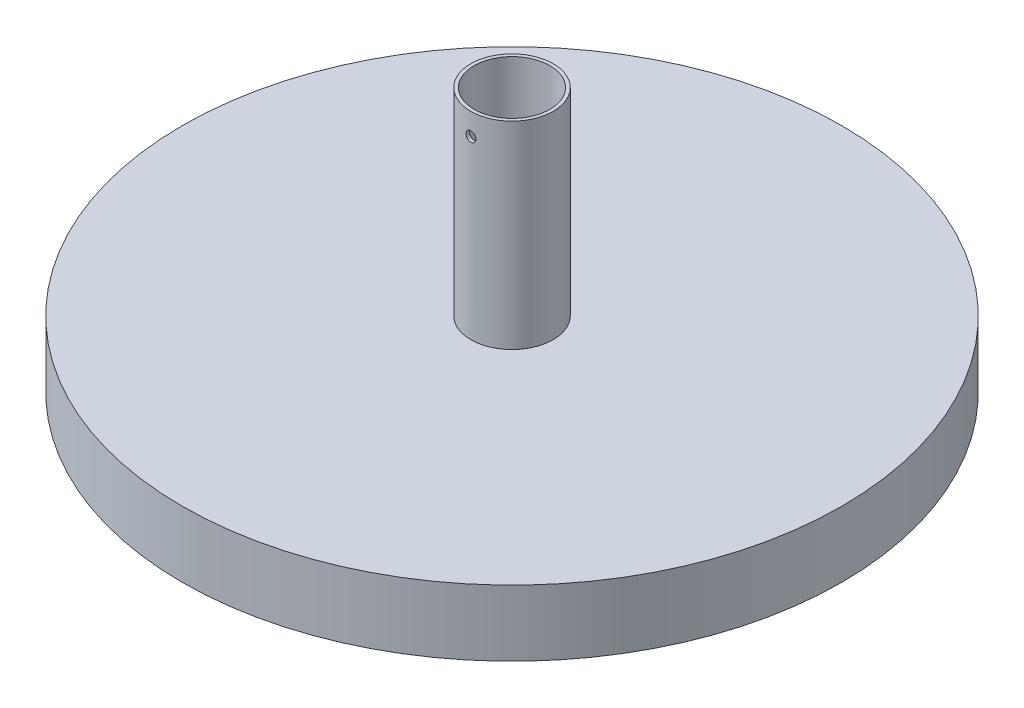
SolidWorks part; units mm, degrees
material "ABS"
ref_plane "Front Plane" through (0, 0, 0) normal (0, 0, 1) x (1, 0, 0)
ref_plane "Top Plane" through (0, 0, 0) normal (0, 1, 0) x (1, 0, 0)
ref_plane "Right Plane" through (0, 0, 0) normal (1, 0, 0) x (0, 0, -1)
sketch "Sketch1" plane through (0, 0, 0) normal (0, 1, 0) x (1, 0, 0)
  circle A0 centre (0, 0) radius 100
  dimension "D1" = 200
extrude "Boss-Extrude1" add sketch "Sketch1" along normal blind 20
sketch "Sketch2" plane through (0, 20, 0) normal (0, 1, 0) x (1, 0, 0)
  circle A0 centre (0, 0) radius 11.5
  circle A1 centre (0, 0) radius 12.5
  dimension "D1" = 23
  dimension "D2" = 25
extrude "Boss-Extrude2" add sketch "Sketch2" along normal blind 60
sketch "Sketch3" plane through (0, 0, 0) normal (0, 0, 1) x (1, 0, 0)
  circle A0 centre (0, 73.3832) radius 1.5
  dimension "D1" = 3
extrude "Cut-Extrude1" cut sketch "Sketch3" along normal up to surface (12.4097 mm away)
